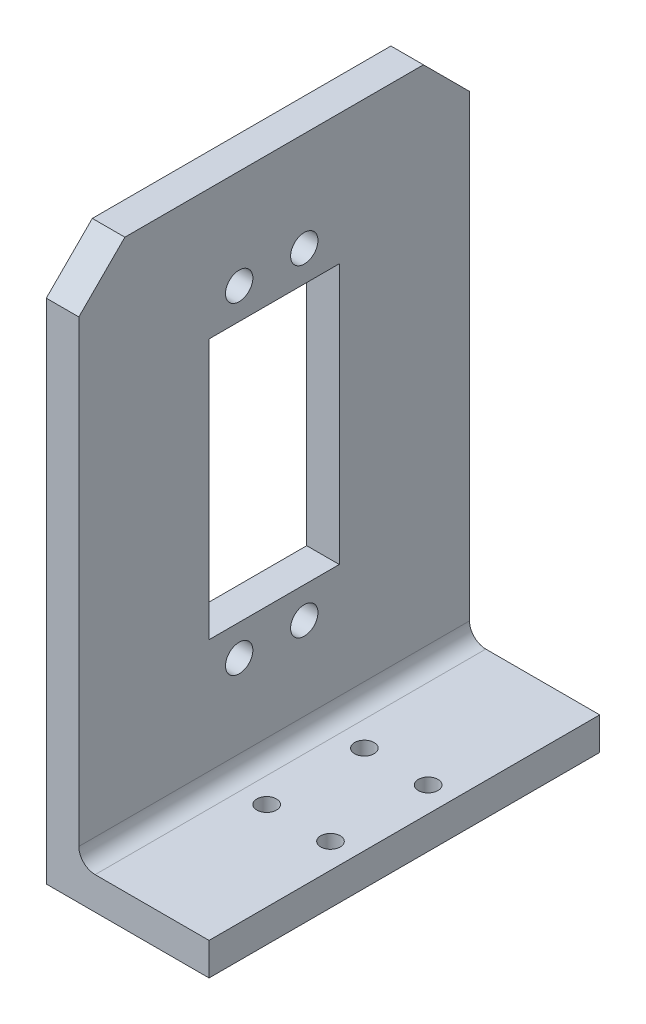
SolidWorks part; units mm, degrees
ref_plane "Front Plane" through (0, 0, 0) normal (0, 0, 1) x (1, 0, 0)
ref_plane "Top Plane" through (0, 0, 0) normal (0, 1, 0) x (1, 0, 0)
ref_plane "Right Plane" through (0, 0, 0) normal (1, 0, 0) x (0, 0, -1)
sketch "Sketch1" plane through (0, 0, 0) normal (0, 1, 0) x (1, 0, 0)
  line L0 (-28.6508, 0) -> (24.4776, 0) construction
  line L1 (-12.5, 30) -> (12.5, 30)
  line L2 (-12.5, 30) -> (-12.5, -30)
  line L3 (-12.5, -30) -> (12.5, -30)
  line L4 (12.5, 30) -> (12.5, -30)
  line L5 (-12.5, 30) -> (12.5, -30) construction
  line L6 (-12.5, -30) -> (12.5, 30) construction
  line L7 (-1.15, 9.9015) -> (-1.15, -43.5479) construction
  point P0 (0, 0)
  point P10 (-1.15, 7.5)
  point P11 (-1.15, -7.5)
  dimension "D1" = 25
  dimension "D2" = 60
  dimension "D3" = 11.35
  dimension "D4" = 15
extrude "Boss-Extrude1" add sketch "Sketch1" along normal blind 5
sketch "Sketch8" plane through (0, 5, 0) normal (0, 1, 0) x (1, 0, 0)
  line L0 (-12.5, -30) -> (12.5, -30) construction
  line L1 (-12.5, 30) -> (-7.5, 30)
  line L2 (-12.5, 30) -> (-12.5, -30)
  line L3 (-12.5, -30) -> (-7.5, -30)
  line L4 (-7.5, 30) -> (-7.5, -30)
  dimension "D1" = 5
extrude "Boss-Extrude2" add sketch "Sketch8" along normal blind 80
sketch "Sketch9" plane through (-7.5, 0, 0) normal (1, 0, 0) x (0, 0, -1)
  line L0 (0, 85) -> (0, 5) construction
  line L1 (-30, 85) -> (30, 85) construction
  line L2 (-30, 5) -> (30, 5) construction
  line L3 (-30, 45) -> (30, 45) construction
  line L4 (-30, 85) -> (-30, 5) construction
  line L5 (30, 85) -> (30, 5) construction
  line L7 (-10, 65) -> (10, 65)
  line L8 (-10, 65) -> (-10, 25)
  line L9 (-10, 25) -> (10, 25)
  line L10 (10, 65) -> (10, 25)
  line L11 (-10, 65) -> (10, 25) construction
  line L12 (-10, 25) -> (10, 65) construction
  circle A0 centre (-5.3745, 69.75) radius 2.1
  circle A1 centre (4.6255, 69.75) radius 2.1
  circle A2 centre (-5.3745, 20.25) radius 2.1
  circle A3 centre (4.6255, 20.25) radius 2.1
  point P12 (0, 45)
  dimension "D3" = 4.2
  dimension "D4" = 4.75
  dimension "D5" = 4.2
  dimension "D6" = 10
  dimension "D7" = 4.2
  dimension "D9" = 4.2
  dimension "D1" = 20
  dimension "D2" = 40
  dimension "D8" = 4.75
  dimension "D10" = 10
extrude "Cut-Extrude1" cut sketch "Sketch9" against normal up to surface (5 mm away) up to face at (-12.5, 42.5, 0)
sketch "Sketch10" plane through (-7.5, 0, 0) normal (1, 0, 0) x (0, 0, -1)
  line L0 (-22.9289, 85) -> (-30, 77.9289)
  line L1 (22.9289, 85) -> (30, 77.9289)
  line L2 (22.9289, 85) -> (30, 85)
  line L3 (-30, 85) -> (-22.9289, 85)
  line L4 (-30, 85) -> (-30, 77.9289)
  line L6 (30, 85) -> (30, 77.9289)
  dimension "D1" = 45
  dimension "D2" = 45
  dimension "D3" = 5
  dimension "D4" = 5
extrude "Cut-Extrude2" cut sketch "Sketch10" against normal up to next
sketch "Sketch18" plane through (-7.5, 0, 0) normal (1, 0, 0) x (0, 0, -1)
  line L0 (-62.1037, 55) -> (62.7901, 55) construction
  line L1 (0, -24.0352) -> (0, 110.2154) construction
  line L2 (-30, 0) -> (30, 0) construction
  line L3 (-30, 0) -> (30, 0) construction
  dimension "D1" = 55
fillet "Fillet1" radius 2.5 1 edges at (-7.5, 5, 0)
ref_plane "Plane1" through (3.75, 0, 0) normal (1, 0, 0) x (0, 0, -1)
hole_wizard "Ø3.0mm Dowel Hole1" positions "Sketch16" profile "Sketch17" hole size "Ø3.0" standard "ANSI Metric" end condition through all
sketch "Sketch16" plane through (0, 5, 0) normal (0, 1, 0) x (1, 0, 0)
  point P0 (-1.15, 7.5)
  point P3 (-1.15, -7.5)
sketch "Sketch17" plane through (-1.15, 5, -7.5) normal (1, 0, 0) x (0, 0, 1)
  line L0 (0, 0) -> (0, 5)
  line L1 (0, 5) -> (1.5, 5)
  line L2 (1.5, 5) -> (1.5, 0)
  line L5 (1.5, 0) -> (0, 0)
  line L11 (0, -6.35) -> (0, 107.95) construction
  dimension "Thru Hole Dia." = 3
  dimension "Thru Hole Depth" = 5
mirror "Mirror1" about plane through (3.75, 0, 0) normal (1, 0, 0) of "Ø3.0mm Dowel Hole1"
equation "\"HeightHole\"=55"
equation "\"D1@Sketch18\"=\"HeightHole\""
